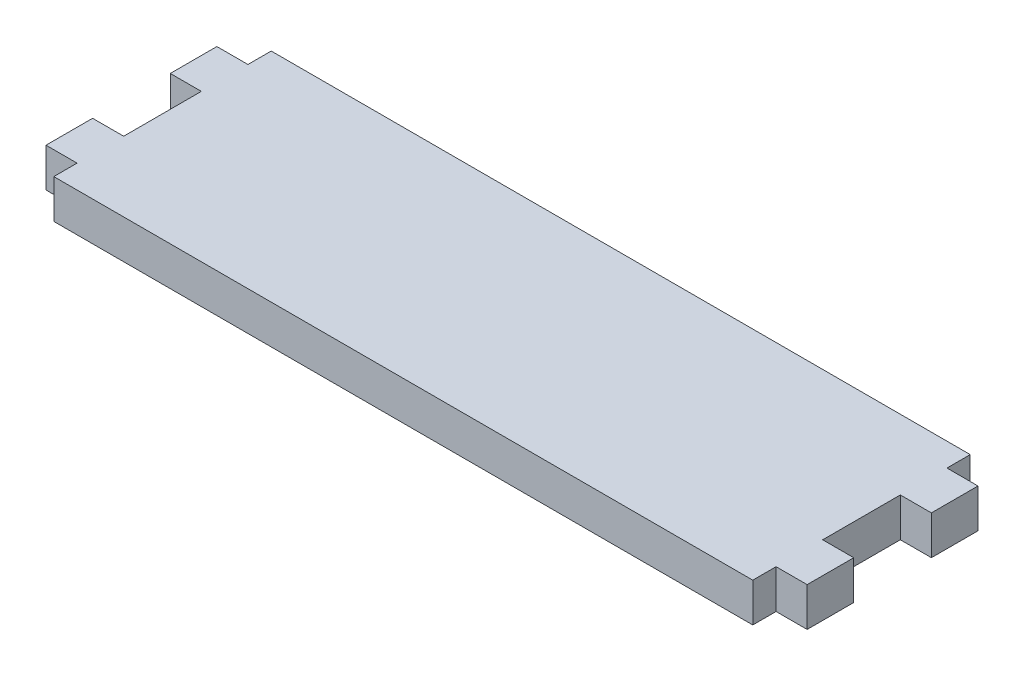
SolidWorks part; units mm, degrees
ref_plane "Front Plane" through (0, 0, 0) normal (0, 0, 1) x (1, 0, 0)
ref_plane "Top Plane" through (0, 0, 0) normal (0, 1, 0) x (1, 0, 0)
ref_plane "Right Plane" through (0, 0, 0) normal (1, 0, 0) x (0, 0, -1)
sketch "Sketch1" plane through (0, 0, 0) normal (0, 1, 0) x (1, 0, 0)
  line L40 (0, 0) -> (0, 3)
  line L41 (0, 3) -> (-4, 3)
  line L42 (-4, 3) -> (-4, 9)
  line L43 (-4, 9) -> (0, 9)
  line L44 (0, 9) -> (0, 19)
  line L45 (0, 19) -> (-4, 19)
  line L46 (-4, 19) -> (-4, 25)
  line L47 (-4, 25) -> (0, 25)
  line L48 (0, 25) -> (0, 28)
  line L49 (0, 28) -> (90, 28)
  line L50 (90, 28) -> (90, 25)
  line L51 (90, 25) -> (94, 25)
  line L52 (94, 25) -> (94, 19)
  line L53 (94, 19) -> (90, 19)
  line L54 (90, 19) -> (90, 9)
  line L55 (90, 9) -> (94, 9)
  line L56 (94, 9) -> (94, 3)
  line L57 (94, 3) -> (90, 3)
  line L58 (90, 3) -> (90, 0)
  line L59 (90, 0) -> (0, 0)
  dimension "D4" = 3
  dimension "D1" = 90
  dimension "D2" = 6
  dimension "D3" = 3
  dimension "D5" = 4
  dimension "D6" = 4
  dimension "D7" = 10
  dimension "D8" = 6
  dimension "D9" = 28
  dimension "D10" = 4
  dimension "D11" = 6
  dimension "D12" = 10
  dimension "D13" = 6
  dimension "D14" = 98
  dimension "D15" = 28
  dimension "D18" = 4
extrude "Boss-Extrude1" add sketch "Sketch1" along normal blind 5
